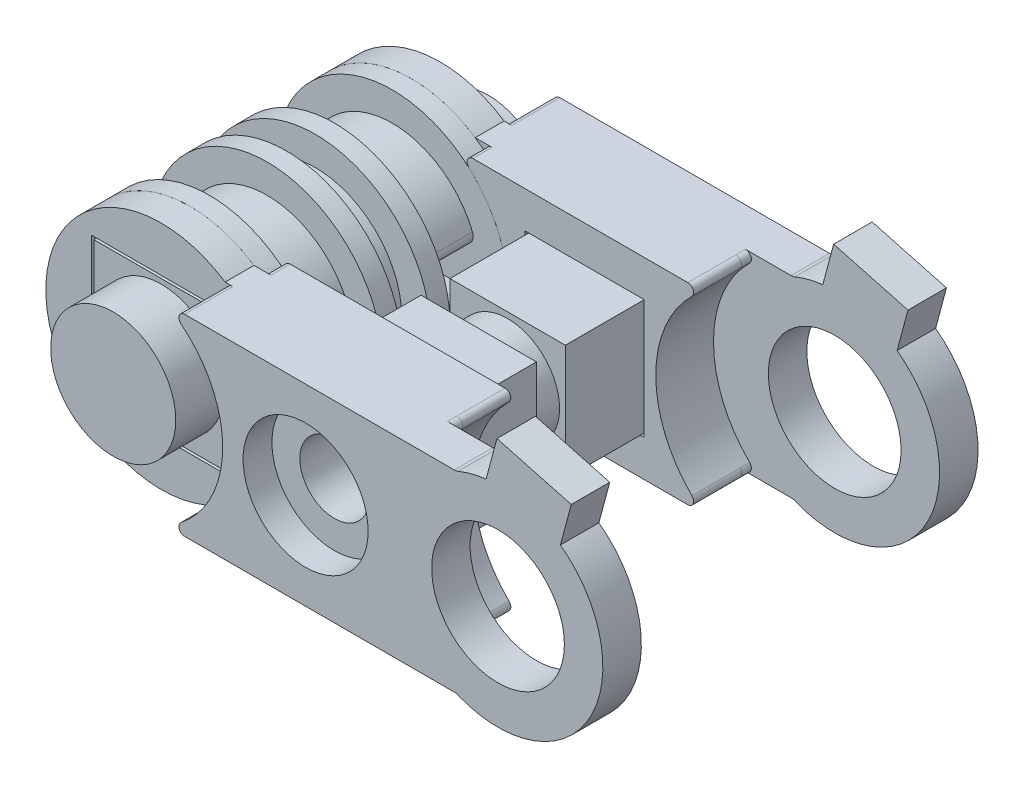
SolidWorks part; units mm, degrees
material "ABS"
ref_plane "正面" through (0, 0, 0) normal (0, 0, 1) x (1, 0, 0)
ref_plane "平面" through (0, 0, 0) normal (0, 1, 0) x (1, 0, 0)
ref_plane "右側面" through (0, 0, 0) normal (1, 0, 0) x (0, 0, -1)
sketch "ｽｹｯﾁ1" plane through (0, 0, 0) normal (0, 0, 1) x (1, 0, 0)
  circle A0 centre (0, 0) radius 4.5
  dimension "D1" = 9
extrude "ﾎﾞｽ - 押し出し1" add sketch "ｽｹｯﾁ1" along normal blind 3
sketch "ｽｹｯﾁ2" plane through (0, 0, 0) normal (0, 0, -1) x (-1, 0, 0)
  circle A0 centre (0, 0) radius 6
  dimension "D1" = 12
extrude "ﾎﾞｽ - 押し出し2" add sketch "ｽｹｯﾁ2" along normal blind 1
sketch "ｽｹｯﾁ3" plane through (0, 0, -1) normal (0, 0, -1) x (-1, 0, 0)
  circle A0 centre (0, 0) radius 4.5 construction
  circle A1 centre (0, 0) radius 4.5
extrude "ﾎﾞｽ - 押し出し3" add sketch "ｽｹｯﾁ3" along normal blind 1.5
sketch "ｽｹｯﾁ4" plane through (0, 0, -2.5) normal (0, 0, -1) x (-1, 0, 0)
  circle A1 centre (0, 0) radius 6
  circle A2 centre (0, 0) radius 6
  dimension "D1" = 0
extrude "ﾎﾞｽ - 押し出し4" add sketch "ｽｹｯﾁ4" along normal blind 1
sketch "ｽｹｯﾁ5" plane through (0, 0, -3.5) normal (0, 0, -1) x (-1, 0, 0)
  circle A0 centre (0, 0) radius 4.5 construction
  circle A1 centre (0, 0) radius 4.5
extrude "ﾎﾞｽ - 押し出し5" add sketch "ｽｹｯﾁ5" along normal blind 3
sketch "ｽｹｯﾁ6" plane through (0, 0, -6.5) normal (0, 0, -1) x (-1, 0, 0)
  circle A1 centre (0, 0) radius 6
  circle A2 centre (0, 0) radius 6
  dimension "D1" = 0
extrude "ﾎﾞｽ - 押し出し6" add sketch "ｽｹｯﾁ6" along normal blind 1
sketch "ｽｹｯﾁ7" plane through (0, 0, 3) normal (0, 0, 1) x (1, 0, 0)
  circle A1 centre (0, 0) radius 6
  circle A2 centre (0, 0) radius 6
  dimension "D1" = 0
extrude "ﾎﾞｽ - 押し出し7" add sketch "ｽｹｯﾁ7" along normal blind 1
sketch "ｽｹｯﾁ10" plane through (0, 0, 4) normal (0, 0, 1) x (1, 0, 0)
  line L1 (3.5, -3.5) -> (-3.5, -3.5)
  line L2 (3.5, -3.5) -> (3.5, 3.5)
  line L3 (3.5, 3.5) -> (-3.5, 3.5)
  line L4 (-3.5, -3.5) -> (-3.5, 3.5)
  line L5 (3.5, -3.5) -> (-3.5, 3.5) construction
  line L6 (3.5, 3.5) -> (-3.5, -3.5) construction
  point P0 (0, 0)
  dimension "D1" = 7
  dimension "D2" = 7
extrude "ﾎﾞｽ - 押し出し10" add sketch "ｽｹｯﾁ10" along normal blind 1.5
sketch "ｽｹｯﾁ11" plane through (0, 0, 5.5) normal (0, 0, 1) x (1, 0, 0)
  circle A0 centre (0, 0) radius 3.25
  dimension "D1" = 6.5
extrude "ﾎﾞｽ - 押し出し11" add sketch "ｽｹｯﾁ11" along normal blind 2.5
ref_plane "平面1" through (0, 0, -1.75) normal (0, 0, 1) x (1, 0, 0)
mirror "ﾐﾗｰ1" about plane through (0, 0, -1.75) normal (0, 0, 1) of "ﾎﾞｽ - 押し出し11", "ﾎﾞｽ - 押し出し10"
sketch "ｽｹｯﾁ12" plane through (0, 0, 4) normal (0, 0, 1) x (1, 0, 0)
  line L0 (0, 0) -> (20, 0) construction
  line L1 (3.3166, 5) -> (16.1672, 5)
  line L3 (16.1672, -5) -> (3.3166, -5)
  line L8 (3.64, -3.64) -> (3.64, 3.64)
  line L9 (-3.64, -3.64) -> (3.64, -3.64)
  line L10 (-3.64, 3.64) -> (-3.64, -3.64)
  line L11 (3.64, 3.64) -> (-3.64, 3.64)
  line L12 (3.64, -3.64) -> (3.64, 3.64)
  line L13 (-3.64, -3.64) -> (3.64, -3.64)
  line L14 (-3.64, 3.64) -> (-3.64, -3.64)
  line L15 (3.64, 3.64) -> (-3.64, 3.64)
  circle A0 centre (0, 0) radius 6 construction
  circle A1 centre (20, 0) radius 3.45 construction
  arc A2 (3.3166, 5) -> (3.3166, -5) centre (0, 0) ccw
  circle A3 centre (20, 0) radius 5.45 construction
  circle A4 centre (20, 0) radius 6.3 construction
  arc A5 (16.1672, 5) -> (16.1672, -5) centre (20, 0) ccw
  circle A6 centre (20, 0) radius 6 construction
  circle A7 centre (0, 0) radius 6 construction
  circle A8 centre (20, 0) radius 3.25 construction
  circle A9 centre (0, 0) radius 3.25 construction
  dimension "D3" = 20
  dimension "D6" = 0.3
  dimension "D2" = 5
  dimension "D7" = 5
  dimension "D4" = 0.2
  dimension "D5" = 2
  dimension "D1" = 0.14
extrude "ﾎﾞｽ - 押し出し12" add sketch "ｽｹｯﾁ12" along normal blind 1.5 separate body
sketch "ｽｹｯﾁ13" plane through (0, 0, 5.5) normal (0, 0, 1) x (1, 0, 0)
  line L6 (16.1672, 5) -> (3.3166, 5) construction
  line L9 (16.1672, 5) -> (3.3166, 5) construction
  line L10 (15.3664, 5) -> (3.7135, 5)
  line L11 (15.3664, -5) -> (3.7135, -5)
  circle A1 centre (0, 0) radius 3.25 construction
  arc A7 (16.1672, 5) -> (16.1672, -5) centre (20, 0) ccw construction
  arc A8 (15.577, 4.4864) -> (15.577, -4.4864) centre (20, 0) ccw
  circle A10 centre (0, 0) radius 5.69 construction
  circle A11 centre (0, 0) radius 3.39 construction
  circle A12 centre (0, 0) radius 5.39 construction
  arc A13 (3.5275, 4.4646) -> (3.5275, -4.4646) centre (0, 0) cw
  arc A14 (15.3664, -5) -> (15.577, -4.4864) centre (15.3664, -4.7) ccw
  arc A15 (15.577, 4.4864) -> (15.3664, 5) centre (15.3664, 4.7) ccw
  arc A16 (3.7135, 5) -> (3.5275, 4.4646) centre (3.7135, 4.7) ccw
  arc A17 (3.5275, -4.4646) -> (3.7135, -5) centre (3.7135, -4.7) ccw
  point P24 (2.7159, 5)
  point P29 (2.7159, -5)
  dimension "D1" = 0.14
  dimension "D3" = 0.3
  dimension "D4" = 2
  dimension "D2" = 0.3
extrude "ﾎﾞｽ - 押し出し13" add sketch "ｽｹｯﾁ13" along normal blind 0.5
fillet "ﾌｨﾚｯﾄ9" radius 0.3 2 edges at (16.1672, -5, 4.75) (16.1672, 5, 4.75)
sketch "ｽｹｯﾁ14" plane through (0, 0, 6) normal (0, 0, 1) x (1, 0, 0)
  line L0 (3.7135, 5) -> (17.7301, 5)
  line L3 (3.7135, -5) -> (17.7301, -5)
  arc A0 (17.7301, 5) -> (17.9208, 5.0378) centre (17.7301, 5.5) ccw
  arc A1 (17.7301, -5) -> (17.9208, -5.0378) centre (17.7301, -5.5) cw
  arc A4 (3.5275, -4.4646) -> (3.7135, -5) centre (3.7135, -4.7) ccw construction
  arc A7 (3.5275, -4.4646) -> (3.5275, 4.4646) centre (0, 0) ccw construction
  arc A8 (3.7135, 5) -> (3.5275, 4.4646) centre (3.7135, 4.7) ccw construction
  arc A9 (3.5275, -4.4646) -> (3.7135, -5) centre (3.7135, -4.7) ccw
  arc A10 (3.7135, 5) -> (3.5275, 4.4646) centre (3.7135, 4.7) ccw
  arc A11 (3.5275, -4.4646) -> (3.5275, 4.4646) centre (0, 0) ccw
  circle A12 centre (20, 0) radius 5.45 construction
  arc A13 (17.9208, 5.0378) -> (17.9208, -5.0378) centre (20, 0) cw
  circle A14 centre (20, 0) radius 3.45 construction
  circle A15 centre (20, 0) radius 3.45
  point P19 (17.8315, -5)
  point P22 (17.8315, 5)
  point P24 (17.8315, 5)
  point P27 (17.8315, -5)
  dimension "D1" = 0.5
extrude "ﾎﾞｽ - 押し出し14" add sketch "ｽｹｯﾁ14" along normal blind 2
sketch "ｽｹｯﾁ15" plane through (0, 0, 4) normal (0, 0, -1) x (-1, 0, 0)
  line L0 (-15.3664, 5) -> (-4.1952, 5)
  line L1 (-3.3166, 5) -> (-16.1672, 5) construction
  line L2 (-15.3664, -5) -> (-4.1952, -5)
  line L3 (-16.1672, -5) -> (-3.3166, -5) construction
  circle A2 centre (0, 0) radius 6 construction
  arc A3 (-3.9955, 4.4762) -> (-3.9955, -4.4762) centre (0, 0) ccw
  arc A7 (-4.1952, -5) -> (-3.9955, -4.4762) centre (-4.1952, -4.7) ccw
  arc A8 (-4.1952, 5) -> (-3.9955, 4.4762) centre (-4.1952, 4.7) cw
  arc A10 (-15.577, -4.4864) -> (-15.3664, -5) centre (-15.3664, -4.7) ccw construction
  arc A11 (-15.577, -4.4864) -> (-15.577, 4.4864) centre (-20, 0) ccw construction
  arc A12 (-15.3664, 5) -> (-15.577, 4.4864) centre (-15.3664, 4.7) ccw construction
  arc A13 (-15.577, -4.4864) -> (-15.3664, -5) centre (-15.3664, -4.7) ccw
  arc A14 (-15.577, -4.4864) -> (-15.577, 4.4864) centre (-20, 0) ccw
  arc A15 (-15.3664, 5) -> (-15.577, 4.4864) centre (-15.3664, 4.7) ccw
  point P26 (-3.3166, -5)
  point P29 (-3.3166, 5)
  dimension "D2" = 0.3
extrude "ﾎﾞｽ - 押し出し15" add sketch "ｽｹｯﾁ15" along normal blind 1
mirror "ﾐﾗｰ2" about plane through (0, 0, -1.75) normal (0, 0, 1) of bodies 116
sketch "ｽｹｯﾁ16" plane through (0, 0, 8) normal (0, 0, 1) x (1, 0, 0)
  line L0 (0, 0) -> (20, 0) construction
  circle A0 centre (20, 0) radius 3.45 construction
  circle A1 centre (10, 0) radius 1.8
  dimension "D1" = 3.6
extrude "ｶｯﾄ - 押し出し1" cut sketch "ｽｹｯﾁ16" against normal through all
sketch "ｽｹｯﾁ17" plane through (0, 0, -6.5) normal (0, 0, 1) x (1, 0, 0)
  line L1 (13.1, -3.1) -> (6.9, -3.1)
  line L2 (13.1, -3.1) -> (13.1, 3.1)
  line L3 (13.1, 3.1) -> (6.9, 3.1)
  line L4 (6.9, -3.1) -> (6.9, 3.1)
  line L5 (13.1, -3.1) -> (6.9, 3.1) construction
  line L6 (13.1, 3.1) -> (6.9, -3.1) construction
  point P0 (10, 0)
  dimension "D2" = 6.2
  dimension "D1" = 6.2
extrude "ｶｯﾄ - 押し出し2" cut sketch "ｽｹｯﾁ17" against normal blind 2
sketch "ｽｹｯﾁ18" plane through (0, 0, 3) normal (0, 0, -1) x (-1, 0, 0)
  line L0 (-7, 3) -> (-13, 3)
  line L5 (-13, 3) -> (-13, -3)
  line L6 (-13, -3) -> (-7, -3)
  line L7 (-7, -3) -> (-7, 3)
  line L8 (-13.1, -3.1) -> (-6.9, -3.1)
  line L9 (-6.9, -3.1) -> (-6.9, 3.1)
  line L10 (-6.9, 3.1) -> (-13.1, 3.1)
  line L11 (-13.1, 3.1) -> (-13.1, -3.1)
  line L12 (-13.1, -3.1) -> (-6.9, -3.1) construction
  line L13 (-6.9, -3.1) -> (-6.9, 3.1) construction
  line L14 (-6.9, 3.1) -> (-13.1, 3.1) construction
  line L15 (-13.1, 3.1) -> (-13.1, -3.1) construction
  dimension "D1" = 0
  dimension "D2" = 0.1
extrude "ﾎﾞｽ - 押し出し16" add sketch "ｽｹｯﾁ18" along normal up to surface (11.5 mm away) up to face at (10, 0, -8.5)
sketch "ｽｹｯﾁ19" plane through (0, 0, 3) normal (0, 0, 1) x (1, 0, 0)
  circle A0 centre (10, 0) radius 1.8 construction
  circle A1 centre (10, 0) radius 1.8
extrude "ｶｯﾄ - 押し出し3" cut sketch "ｽｹｯﾁ19" against normal through all
sketch "ｽｹｯﾁ20" plane through (0, 0, -1.75) normal (0, 0, 1) x (1, 0, 0)
  line L4 (13, 3) -> (7, 3)
  line L5 (13, -3) -> (13, 3)
  line L6 (7, -3) -> (13, -3)
  line L7 (7, 3) -> (7, -3)
  line L8 (13, 3) -> (7, 3)
  line L9 (13, -3) -> (13, 3)
  line L10 (7, -3) -> (13, -3)
  line L11 (7, 3) -> (7, -3)
  circle A1 centre (10, 0) radius 2.7
  dimension "D2" = 5.4
  dimension "D1" = 0
extrude "ｶｯﾄ - 押し出し4" cut sketch "ｽｹｯﾁ20" against normal blind 0.75 and the other way blind 0.75
sketch "ｽｹｯﾁ21" plane through (0, 0, 8) normal (0, 0, 1) x (1, 0, 0)
  circle A0 centre (10, 0) radius 3.25
  dimension "D1" = 6.5
extrude "ｶｯﾄ - 押し出し5" cut sketch "ｽｹｯﾁ21" against normal blind 1.5
sketch "ｽｹｯﾁ22" plane through (0, 0, -11.5) normal (0, 0, -1) x (-1, 0, 0)
  line L1 (-11.6743, 2.9) -> (-13.3486, 0)
  line L2 (-13.3486, 0) -> (-11.6743, -2.9)
  line L3 (-11.6743, -2.9) -> (-8.3257, -2.9)
  line L4 (-8.3257, -2.9) -> (-6.6514, 0)
  line L5 (-6.6514, 0) -> (-8.3257, 2.9)
  line L6 (-8.3257, 2.9) -> (-11.6743, 2.9)
  circle A0 centre (-10, 0) radius 2.9 construction
  dimension "D1" = 5.8
extrude "ｶｯﾄ - 押し出し6" cut sketch "ｽｹｯﾁ22" against normal blind 1
sketch "ｽｹｯﾁ23" plane through (0, 0, 8) normal (0, 0, 1) x (1, 0, 0)
  line L0 (20, 0) -> (21.4106, 5.2643) construction
  line L1 (19.0128, 4.0433) -> (22.8765, 3.008)
  line L2 (19.0128, 4.0433) -> (19.9446, 7.5206)
  line L3 (19.9446, 7.5206) -> (23.8083, 6.4853)
  line L4 (22.8765, 3.008) -> (23.8083, 6.4853)
  line L5 (19.0128, 4.0433) -> (23.8083, 6.4853) construction
  line L6 (19.9446, 7.5206) -> (22.8765, 3.008) construction
  line L7 (20, 0) -> (20, 5.45) construction
  arc A0 (17.9208, -5.0378) -> (17.9208, 5.0378) centre (20, 0) ccw construction
  point P0 (21.4106, 5.2643)
  dimension "D1" = 1.8
  dimension "D2" = 4
  dimension "D3" = 15
extrude "ﾎﾞｽ - 押し出し17" add sketch "ｽｹｯﾁ23" against normal up to surface (2 mm away) up to face at (17.3986, 0, 6)
sketch "ｽｹｯﾁ24" plane through (0, 0, -11.5) normal (0, 0, -1) x (-1, 0, 0)
  line L4 (-22.8765, 3.008) -> (-19.0128, 4.0433)
  line L5 (-23.8083, 6.4853) -> (-22.8765, 3.008)
  line L6 (-19.9446, 7.5206) -> (-23.8083, 6.4853)
  line L7 (-19.0128, 4.0433) -> (-19.9446, 7.5206)
  line L8 (-22.8765, 3.008) -> (-19.0128, 4.0433)
  line L9 (-23.8083, 6.4853) -> (-22.8765, 3.008)
  line L10 (-19.9446, 7.5206) -> (-23.8083, 6.4853)
  line L11 (-19.0128, 4.0433) -> (-19.9446, 7.5206)
  dimension "D1" = 0
extrude "ﾎﾞｽ - 押し出し18" add sketch "ｽｹｯﾁ24" against normal up to surface (2 mm away) up to face at (17.3986, 0, -9.5)
ref_plane "平面2" through (-4.5, 0, 0) normal (-1, 0, 0) x (0, 0, 1)
sketch "ｽｹｯﾁ25" plane through (-4.5, 0, 0) normal (-1, 0, 0) x (0, 0, 1)
  line L0 (-6.5, 0) -> (3, 0) construction
  line L1 (-6.5, -4.5) -> (-6.5, 4.5) construction
  line L2 (3, 4.5) -> (3, -4.5) construction
  line L3 (-3.5, 4.5) -> (-3.5, -4.5) construction
  line L4 (-6.5, -1) -> (-3.5, -1)
  line L5 (-6.5, -1) -> (-6.5, 1)
  line L6 (-6.5, 1) -> (-3.5, 1)
  line L7 (-3.5, -1) -> (-3.5, 1)
  line L8 (0, -4.5) -> (0, 4.5) construction
  line L9 (0, -1) -> (3, -1)
  line L10 (0, -1) -> (0, 1)
  line L11 (0, 1) -> (3, 1)
  line L12 (3, -1) -> (3, 1)
  line L13 (3, 6) -> (3, -6) construction
  dimension "D1" = 2
  dimension "D2" = 1
extrude "ｶｯﾄ - 押し出し7" cut sketch "ｽｹｯﾁ25" against normal through all
fillet "ﾌｨﾚｯﾄ10" radius 0.5 8 edges at (4.3875, -1, 1.5) (-4.3875, -1, 1.5) (-4.3875, 1, 1.5) (4.3875, 1, 1.5) (-4.3875, -1, -5) (4.3875, -1, -5) (4.3875, 1, -5) (-4.3875, 1, -5)
equation "\"D7@ｽｹｯﾁ12\"=\"D2@ｽｹｯﾁ12\""
equation "\"D1@ｽｹｯﾁ17\"=\"D2@ｽｹｯﾁ17\""
equation "\"D2@ｽｹｯﾁ25\"=\"D1@ｽｹｯﾁ25\"/2"
